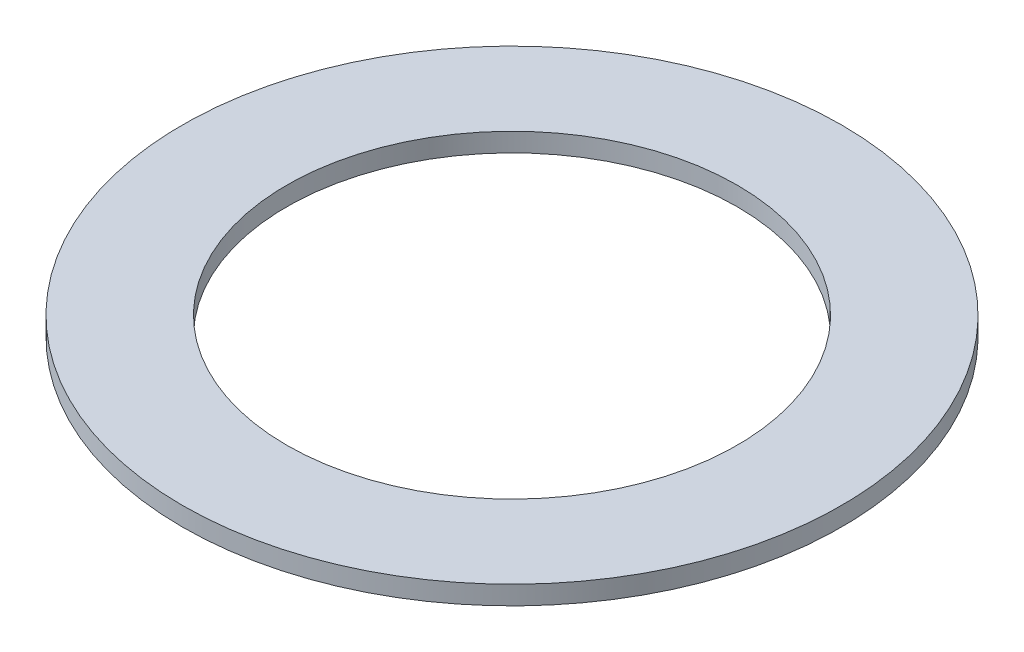
SolidWorks part; units mm, degrees
ref_plane "Front Plane" through (0, 0, 0) normal (0, 0, 1) x (1, 0, 0)
ref_plane "Top Plane" through (0, 0, 0) normal (0, 1, 0) x (1, 0, 0)
ref_plane "Right Plane" through (0, 0, 0) normal (1, 0, 0) x (0, 0, -1)
sketch "Sketch1" plane through (0, 0, 0) normal (0, 1, 0) x (1, 0, 0)
  circle A0 centre (0, 0) radius 17.5551
  circle A1 centre (0, 0) radius 12
  point P5 (0, 0)
extrude "Boss-Extrude1" add sketch "Sketch1" along normal blind 1
